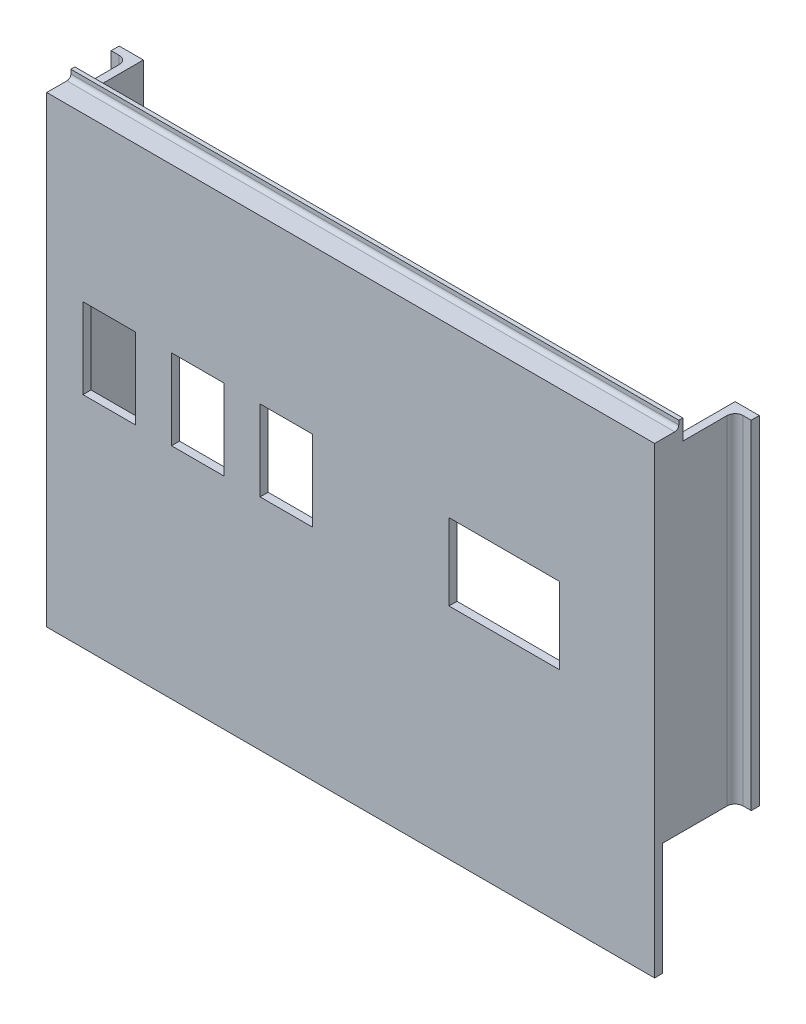
SolidWorks part; units mm, degrees
ref_plane "Front Plane" through (0, 0, 0) normal (0, 0, 1) x (1, 0, 0)
ref_plane "Top Plane" through (0, 0, 0) normal (0, 1, 0) x (1, 0, 0)
ref_plane "Right Plane" through (0, 0, 0) normal (1, 0, 0) x (0, 0, -1)
sketch "Sketch1" plane through (0, 0, 0) normal (0, 0, 1) x (1, 0, 0)
  line L1 (-74.0715, 50.2431) -> (76.9285, 50.2431)
  line L2 (-74.0715, 50.2431) -> (-74.0715, -64.7569)
  line L3 (-74.0715, -64.7569) -> (76.9285, -64.7569)
  line L4 (76.9285, 50.2431) -> (76.9285, -64.7569)
  dimension "D1" = 151
  dimension "D2" = 115
extrude "Boss-Extrude1" add sketch "Sketch1" along normal blind 2
sketch "Sketch2" plane through (0, 0, 2) normal (0, 0, 1) x (1, 0, 0)
  line L0 (1.4285, 50.2431) -> (1.4285, -64.7569) construction
  line L1 (76.9285, 50.2431) -> (-74.0715, 50.2431) construction
  line L2 (-74.0715, -64.7569) -> (76.9285, -64.7569) construction
  line L3 (-74.0715, 50.2431) -> (-74.0715, -64.7569) construction
  line L4 (-65.0715, -19.7569) -> (-52.0715, -19.7569)
  line L5 (-65.0715, -19.7569) -> (-65.0715, -39.7569)
  line L6 (-65.0715, -39.7569) -> (-52.0715, -39.7569)
  line L7 (-52.0715, -19.7569) -> (-52.0715, -39.7569)
  line L8 (-43.0715, -19.7569) -> (-30.0715, -19.7569)
  line L9 (-43.0715, -19.7569) -> (-43.0715, -39.7569)
  line L10 (-43.0715, -39.7569) -> (-30.0715, -39.7569)
  line L11 (-30.0715, -19.7569) -> (-30.0715, -39.7569)
  line L12 (-21.0715, -19.7569) -> (-8.0715, -19.7569)
  line L13 (-21.0715, -19.7569) -> (-21.0715, -39.7569)
  line L14 (-21.0715, -39.7569) -> (-8.0715, -39.7569)
  line L15 (-8.0715, -19.7569) -> (-8.0715, -39.7569)
  dimension "D1" = 13
  dimension "D2" = 20
  dimension "D3" = 25
  dimension "D4" = 25
  dimension "D5" = 25
  dimension "D6" = 9
  dimension "D7" = 9
  dimension "D8" = 9
extrude "Cut-Extrude1" cut sketch "Sketch2" against normal blind 2
sketch "Sketch3" plane through (0, 0, 2) normal (0, 0, 1) x (1, 0, 0)
  line L0 (-8.0715, -29.7569) -> (76.9285, -29.7569) construction
  line L1 (-8.0715, -39.7569) -> (-8.0715, -19.7569) construction
  line L2 (76.9285, -64.7569) -> (76.9285, 50.2431) construction
  line L4 (25.4785, -20.2569) -> (52.9785, -20.2569)
  line L5 (25.4785, -20.2569) -> (25.4785, -39.2569)
  line L6 (25.4785, -39.2569) -> (52.9785, -39.2569)
  line L7 (52.9785, -20.2569) -> (52.9785, -39.2569)
  point P10 (39.2285, -29.7569)
  dimension "D1" = 27.5
  dimension "D2" = 19
  dimension "D3" = 9.5
  dimension "D4" = 37.7
  dimension "D5" = 13.75
extrude "Cut-Extrude2" cut sketch "Sketch3" against normal blind 2
sketch "Sketch4" plane through (0, 0, 0) normal (0, 0, -1) x (-1, 0, 0)
  line L0 (74.0715, 50.2431) -> (74.0715, -64.7569) construction
  line L1 (-76.9285, 50.2431) -> (74.0715, 50.2431)
  line L2 (-76.9285, 50.2431) -> (-76.9285, 47.2431)
  line L3 (-76.9285, 47.2431) -> (74.0715, 47.2431)
  line L4 (74.0715, 50.2431) -> (74.0715, 47.2431)
  dimension "D1" = 3
extrude "Boss-Extrude2" add sketch "Sketch4" along normal blind 4
sketch "Sketch6" plane through (0, 0, -4) normal (0, 0, -1) x (-1, 0, 0)
  line L1 (-76.9285, 47.2431) -> (74.0715, 47.2431)
  line L2 (-76.9285, 47.2431) -> (-76.9285, 52.2431)
  line L3 (-76.9285, 52.2431) -> (74.0715, 52.2431)
  line L4 (74.0715, 47.2431) -> (74.0715, 52.2431)
  dimension "D1" = 5
extrude "Boss-Extrude3" add sketch "Sketch6" along normal blind 1
fillet "Fillet1" radius 1 1 edges
sketch "Sketch7" plane through (0, 0, 0) normal (0, 0, -1) x (-1, 0, 0)
  line L0 (74.0715, -64.7569) -> (-76.9285, -64.7569) construction
  line L1 (-76.9285, 47.2431) -> (-74.9285, 47.2431)
  line L2 (-76.9285, 47.2431) -> (-76.9285, -36.7569)
  line L3 (-76.9285, -36.7569) -> (-74.9285, -36.7569)
  line L4 (-74.9285, 47.2431) -> (-74.9285, -36.7569)
  line L5 (74.0715, 47.2431) -> (72.0715, 47.2431)
  line L6 (74.0715, 47.2431) -> (74.0715, -36.7569)
  line L7 (74.0715, -36.7569) -> (72.0715, -36.7569)
  line L8 (72.0715, 47.2431) -> (72.0715, -36.7569)
  dimension "D1" = 28
  dimension "D2" = 28
  dimension "D3" = 2
  dimension "D4" = 2
extrude "Boss-Extrude4" add sketch "Sketch7" along normal blind 10
sketch "Sketch8" plane through (0, 0, 0) normal (0, 0, -1) x (-1, 0, 0)
  line L1 (-53.3549, -10.2569) -> (-25.8549, -10.2569)
  line L2 (-53.3549, -10.2569) -> (-53.3549, 8.7431)
  line L3 (-53.3549, 8.7431) -> (-25.8549, 8.7431)
  line L4 (-25.8549, -10.2569) -> (-25.8549, 8.7431)
  line L6 (-52.9785, -20.2569) -> (-25.4785, -20.2569) construction
  line L7 (-25.8549, -10.2569) -> (65.0715, -10.2569) construction
  line L8 (52.0715, -19.7569) -> (52.0715, 31.0708) construction
  line L9 (30.0715, -19.7569) -> (30.0715, 31.0708) construction
  line L10 (8.0715, -19.7569) -> (8.0715, 31.0708) construction
  line L13 (8.0715, -10.2569) -> (21.0715, -10.2569)
  line L14 (8.0715, -10.2569) -> (8.0715, 9.7431)
  line L15 (8.0715, 9.7431) -> (21.0715, 9.7431)
  line L16 (21.0715, -10.2569) -> (21.0715, 9.7431)
  line L17 (30.0715, -10.2569) -> (43.0715, -10.2569)
  line L18 (30.0715, -10.2569) -> (30.0715, 9.7431)
  line L19 (30.0715, 9.7431) -> (43.0715, 9.7431)
  line L20 (43.0715, -10.2569) -> (43.0715, 9.7431)
  line L21 (52.0715, -10.2569) -> (65.0715, -10.2569)
  line L22 (52.0715, -10.2569) -> (52.0715, 9.7431)
  line L23 (52.0715, 9.7431) -> (65.0715, 9.7431)
  line L24 (65.0715, -10.2569) -> (65.0715, 9.7431)
  dimension "D1" = 27.5
  dimension "D2" = 19
  dimension "D3" = 10
  dimension "D4" = 13
  dimension "D5" = 13
  dimension "D6" = 20
extrude "Cut-Extrude3" cut sketch "Sketch8" against normal blind 10
sketch "Sketch9" plane through (0, 0, 0) normal (0, 0, -1) x (-1, 0, 0)
  line L1 (-58.0685, -16.6933) -> (68.4441, -16.6933)
  line L2 (-58.0685, -16.6933) -> (-58.0685, -43.6072)
  line L3 (-58.0685, -43.6072) -> (68.4441, -43.6072)
  line L4 (68.4441, -16.6933) -> (68.4441, -43.6072)
extrude "Boss-Extrude5" add sketch "Sketch9" against normal up to surface (2 mm away) up to face at (-36.5715, -0.2569, 2)
sketch "Sketch10" plane through (0, 0, -10) normal (0, 0, -1) x (-1, 0, 0)
  line L1 (-76.9285, 47.2431) -> (-74.9285, 47.2431)
  line L2 (-76.9285, 47.2431) -> (-76.9285, -36.7569)
  line L3 (-76.9285, -36.7569) -> (-74.9285, -36.7569)
  line L4 (-74.9285, 47.2431) -> (-74.9285, -36.7569)
  line L5 (72.0715, -36.7569) -> (74.0715, -36.7569)
  line L6 (72.0715, -36.7569) -> (72.0715, 47.2431)
  line L7 (72.0715, 47.2431) -> (74.0715, 47.2431)
  line L8 (74.0715, -36.7569) -> (74.0715, 47.2431)
extrude "Boss-Extrude6" add sketch "Sketch10" along normal blind 8
sketch "Sketch12" plane through (0, 0, -18) normal (0, 0, -1) x (-1, 0, 0)
  line L1 (-74.9285, 47.2431) -> (-80.9285, 47.2431)
  line L2 (-74.9285, 47.2431) -> (-74.9285, -36.7569)
  line L3 (-74.9285, -36.7569) -> (-80.9285, -36.7569)
  line L4 (-80.9285, 47.2431) -> (-80.9285, -36.7569)
  line L5 (72.0715, -36.7569) -> (78.0715, -36.7569)
  line L6 (72.0715, -36.7569) -> (72.0715, 47.2431)
  line L7 (72.0715, 47.2431) -> (78.0715, 47.2431)
  line L8 (78.0715, -36.7569) -> (78.0715, 47.2431)
  dimension "D1" = 6
  dimension "D2" = 6
extrude "Boss-Extrude7" add sketch "Sketch12" along normal blind 2
fillet "Fillet2" radius 2 1 edges
fillet "Fillet3" radius 2 1 edges
sketch "Sketch14" plane through (0, -36.7569, 0) normal (0, -1, 0) x (-1, 0, 0)
  line L0 (72.0715, 20) -> (78.0715, 20) construction
  line L1 (-76.9285, 0) -> (74.0715, 0)
  line L2 (-76.9285, 0) -> (-76.9285, 20)
  line L3 (-76.9285, 20) -> (74.0715, 20)
  line L4 (74.0715, 0) -> (74.0715, 20)
  line L5 (-76.9285, 20) -> (74.0715, 0) construction
  line L7 (14.2838, 0) -> (-17.1407, 0)
  line L8 (14.2838, 0) -> (14.2838, 20)
  line L9 (14.2838, 20) -> (-17.1407, 20)
  line L10 (-17.1407, 0) -> (-17.1407, 20)
  line L11 (14.2838, 0) -> (-17.1407, 20) construction
  line L12 (14.2838, 20) -> (-17.1407, 0) construction
  point P7 (-1.4285, 10)
  line M2 (-74.9285, 0) -> (-74.9285, 20)
extrude "Boss-Extrude8" add sketch "Sketch14" against normal blind 2 contours L1 L10 L3 M2 | L8 L1 L4 L3
sketch "Sketch15" plane through (0, -34.7569, 0) normal (0, 1, 0) x (1, 0, 0)
  line L0 (74.9285, 0) -> (17.1407, 20) construction
  line L1 (17.1407, 20) -> (-14.2838, 20) construction
  line L2 (-14.2838, 20) -> (-72.0715, 0) construction
  circle A0 centre (46.0346, 10) radius 1.5
  circle A1 centre (-43.1776, 10) radius 1.5
  dimension "D1" = 3
  dimension "D2" = 3
extrude "Cut-Extrude4" cut sketch "Sketch15" against normal blind 2
sketch "Sketch16" plane through (17.1407, 0, 0) normal (-1, 0, 0) x (0, 0, 1)
  line L0 (0, -34.7569) -> (-20, -34.7569)
  line L1 (-20, -34.7569) -> (0, -14.7569)
  line L2 (0, -14.7569) -> (0, -34.7569)
  dimension "D1" = 20
extrude "Boss-Extrude9" add sketch "Sketch16" against normal blind 2
sketch "Sketch18" plane through (-14.2838, 0, 0) normal (1, 0, 0) x (0, 0, -1)
  line L0 (0, -34.7569) -> (20, -34.7569)
  line L1 (20, -34.7569) -> (0, -14.7569)
  line L2 (0, -14.7569) -> (0, -34.7569)
  dimension "D1" = 20
extrude "Boss-Extrude10" add sketch "Sketch18" against normal blind 2
